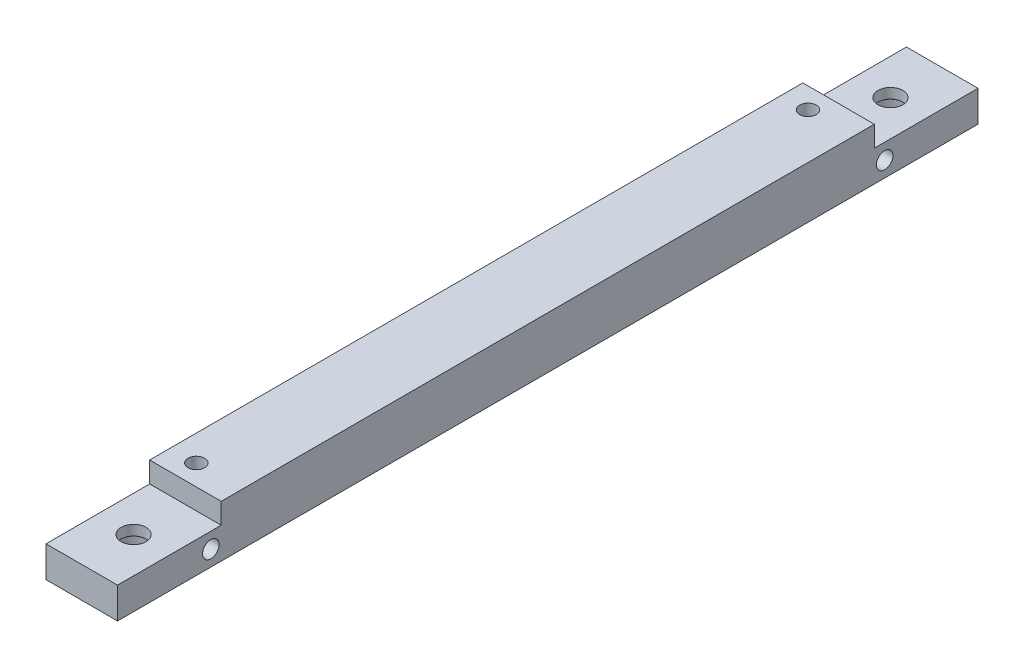
SolidWorks part; units mm, degrees
material "6061-T6 (SS)"
ref_plane "Front Plane" through (0, 0, 0) normal (0, 0, 1) x (1, 0, 0)
ref_plane "Top Plane" through (0, 0, 0) normal (0, 1, 0) x (1, 0, 0)
ref_plane "Right Plane" through (0, 0, 0) normal (1, 0, 0) x (0, 0, -1)
sketch "Sketch1" plane through (0, 0, 0) normal (1, 0, 0) x (0, 0, -1)
  line L1 (0, -2.0984) -> (83, -2.0984)
  line L2 (0, -2.0984) -> (0, -8.0984)
  line L3 (0, -8.0984) -> (83, -8.0984)
  line L4 (83, -2.0984) -> (83, -8.0984)
  dimension "D1" = 83
  dimension "D2" = 6
extrude "Boss-Extrude1" add sketch "Sketch1" along normal blind 8.5
sketch "Sketch7" plane through (0, -2.0984, 0) normal (0, 1, 0) x (1, 0, 0)
  line L0 (0, 83) -> (0, 0) construction
  line L1 (0, 10) -> (8.5, 10)
  line L2 (0, 10) -> (0, 0)
  line L3 (0, 0) -> (8.5, 0)
  line L4 (8.5, 10) -> (8.5, 0)
  line L5 (8.5, 83) -> (0, 83) construction
  dimension "D1" = 73
extrude "Cut-Extrude6" cut sketch "Sketch7" against normal blind 3
sketch "Sketch18" plane through (8.5, 0, 0) normal (1, 0, 0) x (0, 0, -1)
  line L1 (83, -2.0984) -> (73, -2.0984)
  line L2 (83, -2.0984) -> (83, -5.0984)
  line L3 (83, -5.0984) -> (73, -5.0984)
  line L4 (73, -2.0984) -> (73, -5.0984)
  dimension "D1" = 10
extrude "Cut-Extrude8" cut sketch "Sketch18" against normal blind 10
sketch "Sketch21" plane through (0, 0, 0) normal (-1, 0, 0) x (0, 0, 1)
  line L0 (-10, -5.0984) -> (-10, -2.0984) construction
  line L1 (-73, -2.0984) -> (-10, -2.0984)
  line L2 (-73, -2.0984) -> (-73, -3.0984)
  line L3 (-73, -3.0984) -> (-10, -3.0984)
  line L4 (-10, -2.0984) -> (-10, -3.0984)
  dimension "D1" = 1
extrude "Cut-Extrude9" cut sketch "Sketch21" against normal blind 10 contours L3 L4 L1 L2
hole_wizard "M2x0.4 Tapped Hole3" positions "Sketch25" profile "Sketch26" tap size "M2x0.4" standard "BSI" end condition through all
sketch "Sketch25" plane through (0, 0, 0) normal (-1, 0, 0) x (0, 0, 1)
  line L0 (0, -8.0984) -> (-83, -8.0984) construction
  line L1 (-83, -8.0984) -> (-83, -5.0984) construction
  line L2 (0, -5.0984) -> (0, -8.0984) construction
  point P0 (-74, -6.5984)
  point P2 (-9, -6.5984)
  point P9 (0, -6.5984)
  dimension "D1" = 9
  dimension "D2" = 1.5
  dimension "D3" = 9
sketch "Sketch26" plane through (0, -6.5984, -74) normal (0, 1, 0) x (0, 0, 1)
  line L0 (0, 0) -> (0, 8.5)
  line L1 (0, 8.5) -> (0.8, 8.5)
  line L2 (0.8, 8.5) -> (0.8, 0)
  line L5 (0.8, 0) -> (0, 0)
  line L11 (0, -6.35) -> (0, 107.95) construction
  dimension "Thru Tap Drill Dia." = 1.6
  dimension "Thru Tap Drill Depth" = 8.5
cosmetic thread "Hole Thread5" parameters "D2"=2
cosmetic thread "Hole Thread6" parameters "D2"=2
sketch "Sketch27" plane through (0, -8.0984, 0) normal (0, -1, 0) x (1, 0, 0)
  line L0 (8.5, 0) -> (0, 0) construction
  line L1 (0, -83) -> (1.6, -83)
  line L2 (0, -83) -> (0, 0)
  line L3 (0, 0) -> (1.6, 0)
  line L4 (1.6, -83) -> (1.6, 0)
  dimension "D1" = 1.6
extrude "Cut-Extrude12" cut sketch "Sketch27" against normal blind 10
sketch "Sketch30" plane through (0, -8.0984, 0) normal (0, -1, 0) x (1, 0, 0)
  line L0 (8.5, 0) -> (1.6, 0) construction
  line L1 (8.5, -83) -> (1.6, -83) construction
  line L2 (1.6, -83) -> (1.6, 0) construction
  point P0 (5.05, -5)
  point P1 (5.05, -78)
  dimension "D1" = 5
  dimension "D2" = 5
  dimension "D3" = 3.45
  dimension "D4" = 3.45
hole_wizard "CBORE for M2 Socket Head Cap Screw1" positions "Sketch32" profile "Sketch31" counterbore size "M2" standard "JIS" end condition through all
sketch "Sketch32" plane through (0, -8.0984, 0) normal (0, -1, 0) x (-1, 0, 0)
  point P0 (-5.05, 5)
  point P3 (-5.05, 78)
sketch "Sketch31" plane through (5.05, -8.0984, -5) normal (1, 0, 0) x (0, 0, -1)
  line L0 (0, 0) -> (0, 5)
  line L1 (0, 5) -> (1.2, 5)
  line L2 (1.2, 2.025) -> (1.2, 5)
  line L3 (1.2, 2.025) -> (1.225, 2)
  line L4 (1.225, 2) -> (2.2, 2)
  line L5 (2.2, 2) -> (2.2, 0)
  line L7 (0, 0) -> (2.2, 0)
  line L9 (-1.2, 2.025) -> (-1.225, 2) construction
  line L11 (0, -6.35) -> (0, 107.95) construction
  dimension "Thru Hole Dia." = 2.4
  dimension "Thru Hole Depth" = 5
  dimension "C'Bore Dia." = 4.4
  dimension "C'Bore Depth" = 2
  dimension "Mid C'Sink Dia." = 2.45
  dimension "Mid C'Sink Angle" = 90
sketch "Sketch33" plane through (0, -8.0984, 0) normal (0, -1, 0) x (1, 0, 0)
  line L1 (8.5, 0) -> (1.6, 0) construction
  line L2 (8.5, -83) -> (1.6, -83) construction
  line L3 (1.6, -83) -> (1.6, 0) construction
  point P0 (4.1, -71)
  point P5 (4.1, -12)
  dimension "D1" = 2.5
  dimension "D2" = 12
  dimension "D3" = 2.5
  dimension "D4" = 12
hole_wizard "M2x0.4 Tapped Hole2" positions "Sketch35" profile "Sketch34" tap size "M2x0.4" standard "BSI" end condition through all
sketch "Sketch35" plane through (0, -8.0984, 0) normal (0, -1, 0) x (-1, 0, 0)
  point P0 (-4.1, 71)
  point P3 (-4.1, 12)
sketch "Sketch34" plane through (4.1, -8.0984, -71) normal (1, 0, 0) x (0, 0, -1)
  line L0 (0, 0) -> (0, 5)
  line L1 (0, 5) -> (0.8, 5)
  line L2 (0.8, 5) -> (0.8, 0)
  line L5 (0.8, 0) -> (0, 0)
  line L11 (0, -6.35) -> (0, 107.95) construction
  dimension "Thru Tap Drill Dia." = 1.6
  dimension "Thru Tap Drill Depth" = 5
cosmetic thread "Hole Thread7" parameters "D2"=2
cosmetic thread "Cosmetic Thread1" parameters "D2"=2
